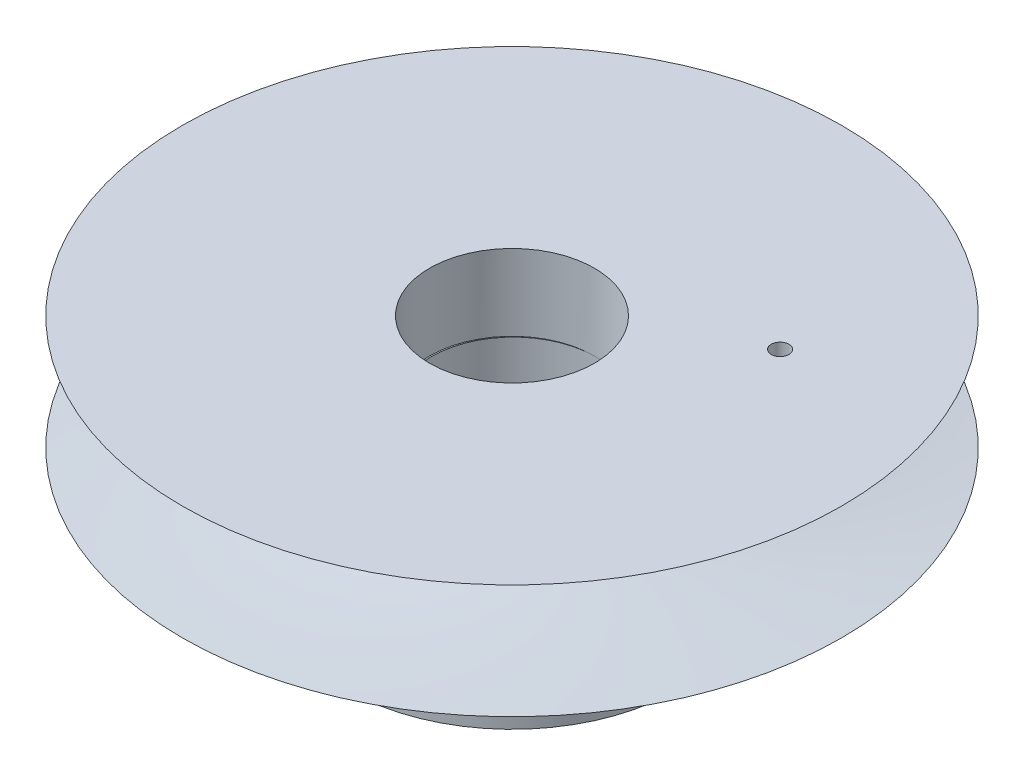
SolidWorks part; units mm, degrees
ref_plane "Front Plane" through (0, 0, 0) normal (0, 0, 1) x (1, 0, 0)
ref_plane "Top Plane" through (0, 0, 0) normal (0, 1, 0) x (1, 0, 0)
ref_plane "Right Plane" through (0, 0, 0) normal (1, 0, 0) x (0, 0, -1)
sketch "Sketch9" plane through (0, 0, 0) normal (0, 0, 1) x (1, 0, 0)
  line L0 (-4.7031, 1.5646) -> (8.2969, -1.4354) construction
  line L1 (-4.7031, -2.9354) -> (8.2969, -2.9354)
  line L3 (-4.7031, 1.5646) -> (8.2969, 1.5646)
  line L4 (8.2969, -2.9354) -> (8.2969, 1.5646)
  line L5 (8.2969, -1.4354) -> (-4.7031, -2.9354) construction
  spline S0 degree 2 poles (-4.7031, 1.5646) (8.2969, -1.4354) (-4.7031, -2.9354) knots 0 0 0 1 1 1
  dimension "D3" = 13
  dimension "D1" = 4.5
  dimension "D2" = 13
revolve "Revolve1" add sketch "Sketch9" angle 360 about L4
sketch "Sketch117" plane through (0, 1.5646, 0) normal (0, 1, 0) x (1, 0, 0)
  circle A0 centre (8.2969, 0) radius 3.25
extrude "Cut-Extrude4" cut sketch "Sketch117" against normal blind 3
sketch "Sketch122" plane through (0, -2.9354, 0) normal (0, -1, 0) x (-1, 0, 0)
  circle A0 centre (-8.2969, 0) radius 6.5398
extrude "Boss-Extrude1" add sketch "Sketch122" along normal blind 5
hole_wizard "M2x0.4 Tapped Hole1" positions "3DSketch1" profile "Sketch124" tap size "M2x0.4" standard "ANSI Metric" end condition through all
sketch3d "3DSketch1"
  circle A0 centre (8.2969, -2.9354, 0) radius 6.5398 construction
  circle A1 centre (8.2969, -7.9354, 0) radius 6.5398 construction
  point P0 (1.8154, -5.4316, -0.8709)
  point P5 (8.2969, -9.4751, 0)
  point P8 (8.2969, -14.4751, 0)
  dimension "D1" = 7
  dimension "D2" = 7.0027
sketch "Sketch124" plane through (1.8154, -5.4316, -0.8709) normal (0, 1, 0) x (-0.1332, 0, 0.9911)
  line L0 (0, 0) -> (0, 21.1551)
  line L1 (0, 21.1551) -> (0.8, 21.1551)
  line L2 (0.8, 21.1551) -> (0.8, 0)
  line L5 (0.8, 0) -> (0, 0)
  line L11 (0, -6.35) -> (0, 107.95) construction
  dimension "Thru Tap Drill Dia." = 1.6
  dimension "Thru Tap Drill Depth" = 21.1551
cosmetic thread "Hole Thread1" parameters "D2"=2
sketch "Sketch125" plane through (0, -1.4354, 0) normal (0, 1, 0) x (1, 0, 0)
  circle A0 centre (8.3503, 0) radius 3.25
extrude "Cut-Extrude5" cut sketch "Sketch125" against normal blind 7
sketch "Sketch126" plane through (0, 1.5646, 0) normal (0, 1, 0) x (1, 0, 0)
  circle A0 centre (14.7307, 4.1367) radius 0.35
  point P2 (12.912, 4.9632)
  point P3 (14.1643, 4.3691)
  point P4 (14.7307, 4.1367)
  dimension "D1" = 0.7
extrude "Cut-Extrude6" cut sketch "Sketch126" against normal blind 2
